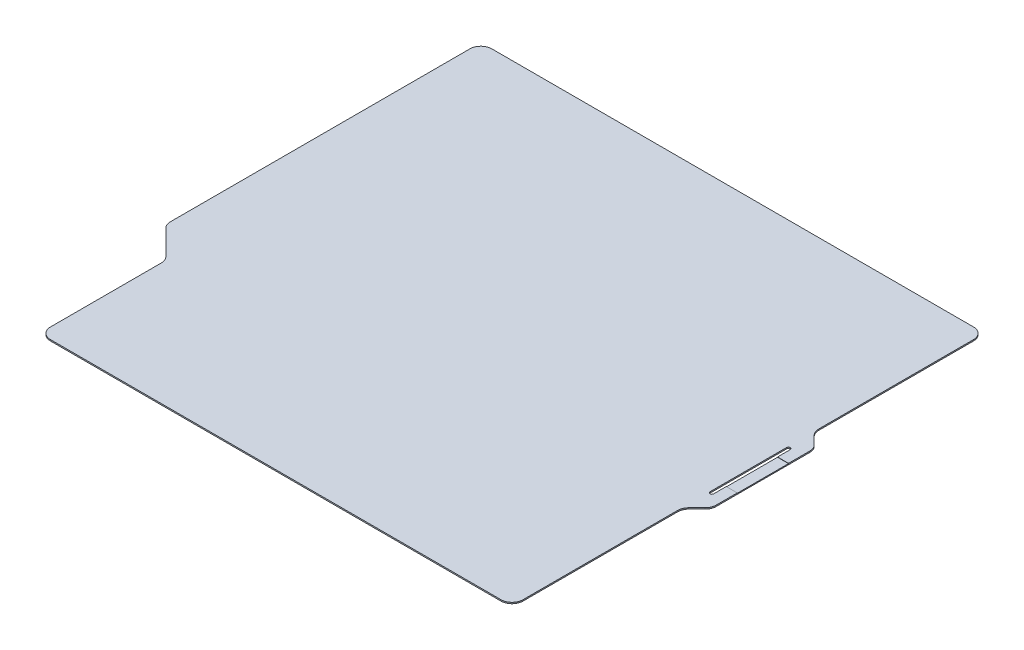
SolidWorks part; units mm, degrees
ref_plane "Front Plane" through (0, 0, 0) normal (0, 0, 1) x (1, 0, 0)
ref_plane "Top Plane" through (0, 0, 0) normal (0, 1, 0) x (1, 0, 0)
ref_plane "Right Plane" through (0, 0, 0) normal (1, 0, 0) x (0, 0, -1)
sketch "Sketch1" plane through (0, 0, 0) normal (0, 1, 0) x (1, 0, 0)
  line L0 (-146, -43) -> (-129, -60)
  line L1 (129, 129) -> (-129, 129)
  line L2 (129, 129) -> (129, -129)
  line L3 (129, -129) -> (-129, -129)
  line L4 (-129, 129) -> (-129, -129)
  line L5 (0, -129) -> (0, 129) construction
  line L6 (129, 0) -> (-129, 0) construction
  line L7 (129, 28) -> (137, 28)
  line L8 (129, 28) -> (129, -28)
  line L9 (129, -28) -> (137, -28)
  line L10 (137, 28) -> (137, -28)
  line L11 (133, -28) -> (133, 28) construction
  line L12 (129, 0) -> (137, 0) construction
  line L13 (-129, 129) -> (-146, 129)
  line L14 (-129, 129) -> (-129, -43)
  line L15 (-129, -43) -> (-146, -43)
  line L16 (-146, 129) -> (-146, -43)
  line L17 (-137.5, -43) -> (-137.5, 129) construction
  line L18 (-129, 43) -> (-146, 43) construction
  line L19 (137, 28) -> (129, 36)
  line L20 (137, -28) -> (129, -36)
  point P0 (0, 0)
  point P71 (-137.5, 43)
  point P208 (133, 0)
  dimension "D1" = 45
  dimension "D2" = 258
  dimension "D3" = 258
  dimension "D4" = 283
  dimension "D5" = 275
  dimension "D6" = 172
  dimension "D7" = 72
  dimension "D8" = 45
extrude "Boss-Extrude1" add sketch "Sketch1" along normal blind 0.69 contours L13 L16 L15 L4 | L4 L15 L0 | L1 L4 L3 L2 | L20 L9 L2 | L10 L7 L2 L9 | L7 L19 L2
sketch "Sketch2" plane through (0, 0.69, 0) normal (0, 1, 0) x (1, 0, 0)
  line L0 (130, 20.875) -> (130, -20.875) construction
  line L1 (131, 20.875) -> (131, -20.875)
  line L2 (129, 20.875) -> (129, -20.875)
  line L3 (137, 28) -> (137, -28) construction
  line L4 (130, 0) -> (0, 0) construction
  arc A0 (131, 20.875) -> (129, 20.875) centre (130, 20.875) ccw
  arc A1 (129, -20.875) -> (131, -20.875) centre (130, -20.875) ccw
  point P2 (130, 0)
  point P11 (0, 0)
  dimension "D3" = 43.75
  dimension "D1" = 2
  dimension "D2" = 6
extrude "Cut-Extrude1" cut sketch "Sketch2" against normal through all
sketch "Sketch3" plane through (0, 0.69, 0) normal (0, 1, 0) x (1, 0, 0)
  line L0 (131, -20.875) -> (131, 20.875) construction
  line L1 (131, 14) -> (137, 14)
  line L2 (131, 14) -> (131, -14)
  line L3 (131, -14) -> (137, -14)
  line L4 (137, 14) -> (137, -14)
  line L5 (134, -14) -> (134, 14) construction
  line L6 (131, 0) -> (137, 0) construction
  line L7 (137, 28) -> (137, -28) construction
  point P8 (137, 0)
  point P204 (134, 0)
  dimension "D1" = 28
extrude "Cut-Extrude2" cut sketch "Sketch3" against normal offset from surface (0.14 mm away) 0.55 up to face at (130, 0, 0)
fillet "Fillet1" radius 6 10 edges at (137, 0.345, 28) (137, 0.345, -28) (129, 0.345, -36) (-146, 0.345, -129) (-146, 0.345, 43) (-129, 0.345, 60) (-129, 0.345, 129) (129, 0.345, 36) (129, 0.345, -129) (129, 0.345, 129)
